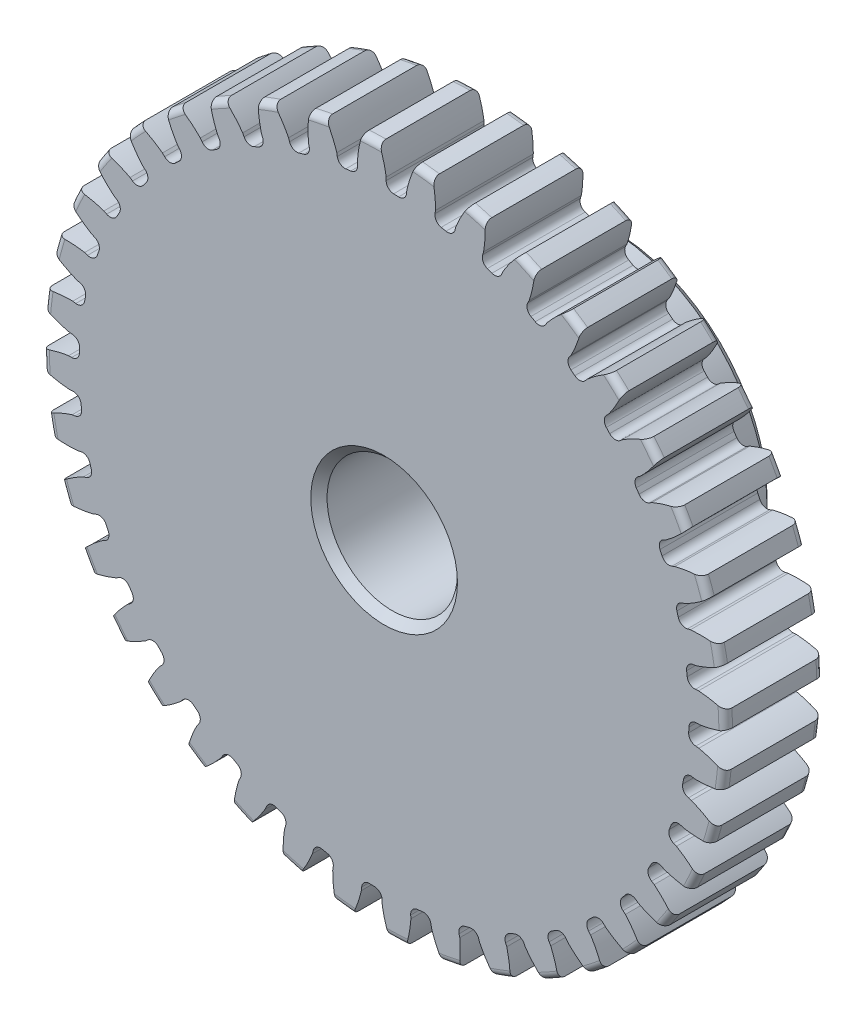
SolidWorks part; units mm, degrees
ref_plane "Front" through (0, 0, 0) normal (0, 0, 1) x (1, 0, 0)
ref_plane "Top" through (0, 0, 0) normal (0, 1, 0) x (1, 0, 0)
ref_plane "Right" through (0, 0, 0) normal (1, 0, 0) x (0, 0, -1)
sketch "Sketch1" plane through (0, 0, 0) normal (0, 0, 1) x (1, 0, 0)
  line L0 (-508, 0) -> (508, 0) construction
  circle A0 centre (0, 0) radius 16.637
  circle A1 centre (0, 0) radius 15.875 construction
  circle A3 centre (0, 0) radius 14.8511 construction
  dimension "D1" = 1.7859
  dimension "OD" = 33.274
  dimension "Ptich Dia" = 31.75
  dimension "Root Dia" = 29.7021
  dimension "D3" = 0.762
  dimension "Number of Teeth" = 1016
extrude "Boss-Extrude1" add sketch "Sketch1" against normal blind 4.7625
sketch "Sketch2" plane through (0, 0, 0) normal (1, 0, 0) x (0, 0, -1)
  line L0 (4.7625, 0) -> (11.1125, 0)
  line L1 (4.7625, 0) -> (4.7625, 7.9375)
  line L2 (4.7625, 7.9375) -> (11.1125, 7.9375)
  line L3 (11.1125, 7.9375) -> (11.1125, 0)
  point P5 (11.1125, -7.9375)
  point P6 (0, -16.637)
  point P7 (4.7625, -16.637)
  point P9 (0, 16.637)
  dimension "Face Wd" = 4.7625
  dimension "B Hub Dia" = 15.875
  dimension "D O'all Lg." = 11.1125
revolve "Revolve1" add sketch "Sketch2" angle 360 about L0
fillet "Fillet2" radius 0.3327 3 edges at (16.637, 0, -4.7625) (16.637, 0, 0) (7.9375, 0, -4.7625)
sketch "Sketch3" plane through (0, 0, 0) normal (0, 0, 1) x (1, 0, 0)
  line L0 (0, 0) -> (0, 16.637) construction
  line L1 (-3.8482, 14.8798) -> (0, 15.875)
  line L2 (-9.5921, 15.875) -> (9.5921, 15.875) construction
  line L3 (-9.2865, 13.4733) -> (9.2865, 18.2767) construction
  line L4 (-3.8482, 14.8798) -> (0, 0) construction
  line L5 (-9.8154, 11.8269) -> (0, 0) construction
  line L6 (-9.8154, 11.8269) -> (-1.5766, 18.6644) construction
  line L7 (-2.6833, 15.1333) -> (0, 0) construction
  line L8 (-2.6833, 15.1333) -> (0.0563, 15.6191) construction
  arc A0 (-3.8482, 14.8798) -> (-9.8154, 11.8269) centre (0, 0) ccw
  circle A1 centre (0, 0) radius 15.875 construction
  circle A2 centre (0, 0) radius 15.3693 construction
  arc A3 (-3.8482, 14.8798) -> (-2.6833, 15.1333) centre (0, 0) cw
  circle A4 centre (0, 0) radius 16.637 construction
  point P6 (0, 15.875)
  dimension "D1" = 3.9748
  dimension "Pressure Angle" = 14.5
  dimension "D2" = 6.7571
  dimension "D3" = 10.7065
  dimension "D4" = 1.1924
  dimension "D5" = 2.7823
sketch "Sketch4" plane through (0, 0, 0) normal (0, 0, 1) x (1, 0, 0)
  line L0 (0, 0) -> (0.6228, 15.8505) construction
  line L1 (0.0999, 15.369) -> (0.0999, 14.8507)
  line L2 (0, 15.875) -> (1.2455, 15.8261) construction
  line L3 (1.1063, 15.3295) -> (1.0656, 14.8128)
  line L4 (0.0999, 14.8507) -> (0, 0) construction
  line L5 (0, 0) -> (0, 16.637) construction
  line L6 (-9.8154, 11.8269) -> (-1.5766, 18.6644) construction
  line L7 (-9.8154, 11.8269) -> (-1.5766, 18.6644) construction
  arc A0 (1.0656, 14.8128) -> (0.0999, 14.8507) centre (0, 0) ccw
  arc A1 (0, 15.875) -> (1.2455, 15.8261) centre (0, 0) cw construction
  circle A2 centre (0, 0) radius 15.875 construction
  circle A3 centre (0, 0) radius 15.3693 construction
  circle A4 centre (0, 0) radius 14.8511 construction
  arc A5 (3.0362, 18.4832) -> (-1.5766, 18.6644) centre (0, 0) ccw
  spline S0 degree 2 poles (-1.5766, 18.6644) (-0.1802, 17.2094) (0.0999, 15.369) knots 0 0 0 1 1 1
  spline S1 degree 2 poles (3.0362, 18.4832) (1.5298, 17.1422) (1.1063, 15.3295) knots 0 0 0 1 1 1
  dimension "D1" = 1.2468
extrude "Cut-Extrude1" cut sketch "Sketch4" against normal through all
fillet "Fillet1" radius 0.374 2 edges at (1.0656, 14.8128, -2.3813) (0.0999, 14.8507, -2.3813)
pattern_circular "CirPattern1" count 40 over 360 about axis through (0, 0, -4.7625) along (0, 0, 1) of "Cut-Extrude1", "Fillet1"
sketch "Sketch5" plane through (0, 0, 0) normal (0, 0, 1) x (1, 0, 0)
  circle A0 centre (0, 0) radius 3.175
  circle A1 centre (0, 0) radius 1.5875 construction
  dimension "Bore Min" = 6.35
  dimension "Bore Max" = 3.175
extrude "Cut-Extrude2" cut sketch "Sketch5" against normal through all
chamfer "Chamfer1" distance 0.3969 angle 45 3 edges at (7.9375, 0, -11.1125) (3.175, 0, 0) (3.175, 0, -11.1125)
sketch "Pitch Dia" plane through (0, 0, 0) normal (0, 0, 1) x (1, 0, 0)
  circle A0 centre (0, 0) radius 15.875 construction
  circle A1 centre (0, 0) radius 15.875 construction
equation "\"D1@Boss-Extrude1\" = \"Face Wd@Sketch2\""
equation "\"D2@Sketch3\" = \"D1@Sketch3\"*1.7"
equation "\"D3@Sketch3\" = \"D1@Sketch3\"+\"D2@Sketch3\"-.001"
equation "\"D4@Sketch3\" = \"D1@Sketch3\"*.3"
equation "\"D5@Sketch3\" = \"D1@Sketch3\"-\"D4@Sketch3\""
equation "\"D1@Sketch4\" = 1.5708/(\"Number of Teeth@Sketch1\"/\"Ptich Dia@Sketch1\")"
equation "\"D1@Chamfer1\" = \"B Hub Dia@Sketch2\"*.025"
equation "\"D1@CirPattern1\" = \"Number of Teeth@Sketch1\""
equation "\"D1@Fillet1\" = \"D1@Sketch4\"*.3"
equation "\"D1@Fillet2\" = \"OD@Sketch1\"*.01"
equation "\"D1@Sketch1\" = 2.250/(\"Number of Teeth@Sketch1\"/\"Ptich Dia@Sketch1\")"
